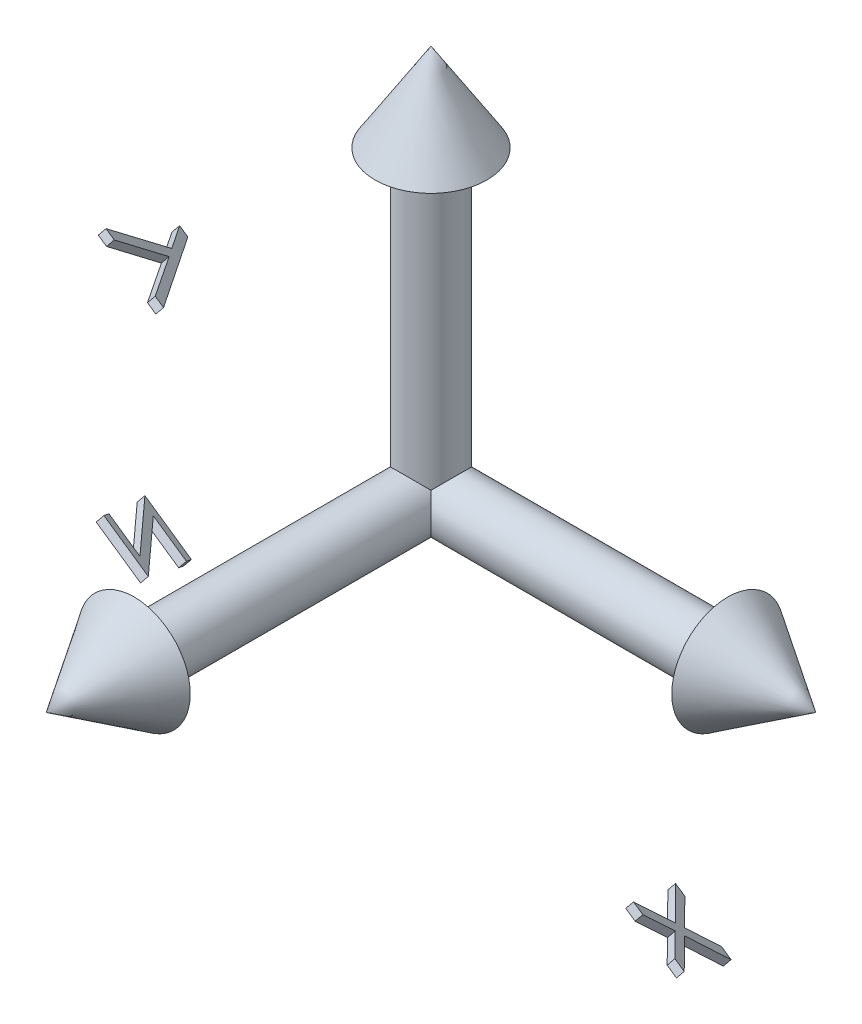
SolidWorks part; units mm, degrees
material "Plain Carbon Steel"
ref_plane "Top Plane" through (0, 0, 0) normal (0, 0, 1) x (1, 0, 0)
ref_plane "Front Plane" through (0, 0, 0) normal (0, 1, 0) x (1, 0, 0)
ref_plane "Right Plane" through (0, 0, 0) normal (1, 0, 0) x (0, 0, -1)
sketch "Sketch2" plane through (0, 0, 0) normal (0, 0, 1) x (1, 0, 0)
  line L0 (0, 0) -> (-39.6671, 0) construction
sketch "Sketch3" plane through (0, 0, 0) normal (0, 1, 0) x (1, 0, 0)
  line L0 (0, 0) -> (0, -3.6459)
  line L1 (0, -3.6459) -> (37.5912, -3.6459)
  line L2 (37.5912, -3.6459) -> (37.5912, -7.0911)
  line L3 (37.5912, -7.0911) -> (48.7474, 0)
  line L4 (48.7474, 0) -> (0, 0)
revolve "Revolve1" add sketch "Sketch3" angle 360 about L4
move or copy body "Body-Move/Copy1" bodies to move or copy 103 copy yes number of copies 1 rotation origin (0, 0, 0) rotation axis (0, -1, 0) rotation angle 90
move or copy body "Body-Move/Copy2" bodies to move or copy 103 copy yes number of copies 1 rotation origin (0, 0, 0) rotation axis (0, 0, 1) rotation angle 90
sketch3d "3DSketch1"
  line L0 (0, 0, 0) -> (-49.8954, -72.1426, 48.0198) construction
  dimension "D1" = 100
ref_plane "Plane2" through (0, 0, 0) normal (-0.499, -0.7214, 0.4802) x (-0.8666, 0.4154, -0.2765)
sketch "Sketch4" plane through (0, 0, 0) normal (-0.499, -0.7214, 0.4802) x (-0.8666, 0.4154, -0.2765)
  line L0 (-42.7918, 6.9401) -> (-56.5467, 11.541) construction
  line L1 (-7.3322, -48.8121) -> (-18.0164, -45.2383) construction
  line L2 (27.8862, -23.2846) -> (18.1888, -20.0409) construction
  text T0 "x" font "Century Gothic" height in points 48
  text T1 "z" font "Century Gothic" height in points 48
  text T2 "y" font "Century Gothic" height in points 48
extrude "Boss-Extrude1" add sketch "Sketch4" along normal blind 1 separate body
